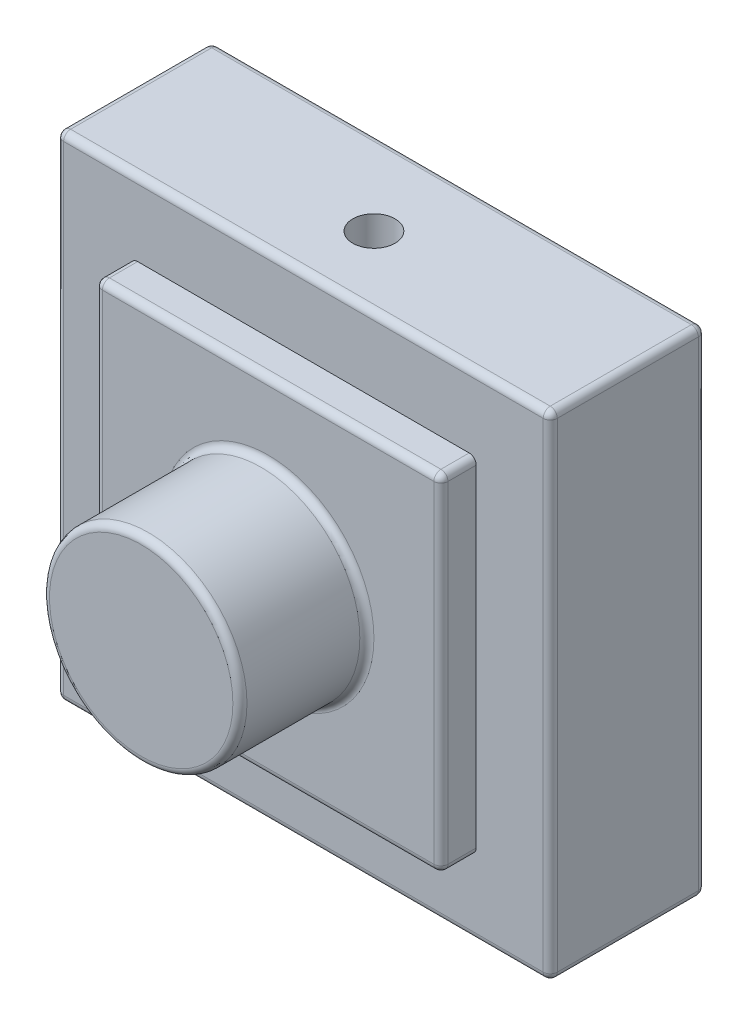
SolidWorks part; units mm, degrees
ref_plane "Front Plane" through (0, 0, 0) normal (0, 0, 1) x (1, 0, 0)
ref_plane "Top Plane" through (0, 0, 0) normal (0, 1, 0) x (1, 0, 0)
ref_plane "Right Plane" through (0, 0, 0) normal (1, 0, 0) x (0, 0, -1)
sketch "Sketch1" plane through (0, 0, 0) normal (0, 0, 1) x (1, 0, 0)
  line L1 (-17.5, 17.5) -> (17.5, 17.5)
  line L2 (-17.5, 17.5) -> (-17.5, -17.5)
  line L3 (-17.5, -17.5) -> (17.5, -17.5)
  line L4 (17.5, 17.5) -> (17.5, -17.5)
  line L5 (-17.5, 17.5) -> (17.5, -17.5) construction
  line L6 (-17.5, -17.5) -> (17.5, 17.5) construction
  point P0 (0, 0)
  dimension "D1" = 35
  dimension "D2" = 35
extrude "Boss-Extrude1" add sketch "Sketch1" along normal blind 11
sketch "Sketch2" plane through (0, 17.5, 0) normal (0, 1, 0) x (1, 0, 0)
  line L0 (0, 0) -> (0, -6) construction
  circle A0 centre (0, -6) radius 1.5
  dimension "D2" = 3
  dimension "D1" = 6
extrude "Cut-Extrude1" cut sketch "Sketch2" against normal blind 5
ref_plane "Plane4" through (0, 0, 0) normal (0, 1, 0) x (1, 0, 0)
mirror "Mirror1" about plane through (0, 0, 0) normal (0, 1, 0) of "Cut-Extrude1"
sketch "Sketch3" plane through (0, 0, 11) normal (0, 0, 1) x (1, 0, 0)
  line L1 (-12.25, 12.25) -> (12.25, 12.25)
  line L2 (-12.25, 12.25) -> (-12.25, -12.25)
  line L3 (-12.25, -12.25) -> (12.25, -12.25)
  line L4 (12.25, 12.25) -> (12.25, -12.25)
  line L5 (-12.25, 12.25) -> (12.25, -12.25) construction
  line L6 (-12.25, -12.25) -> (12.25, 12.25) construction
  point P0 (0, 0)
  dimension "D1" = 24.5
  dimension "D2" = 24.5
extrude "Boss-Extrude2" add sketch "Sketch3" along normal blind 2.5
sketch "Sketch4" plane through (0, 0, 13.5) normal (0, 0, 1) x (1, 0, 0)
  circle A0 centre (0, 0) radius 7
  dimension "D1" = 14
extrude "Boss-Extrude3" add sketch "Sketch4" along normal blind 9
fillet "Fillet1" radius 0.5 21 edges at (17.5, 0, 11) (17.5, 0, 0) (-17.5, 0, 0) (0, 17.5, 0) (0, -17.5, 0) (0, -17.5, 11) (-17.5, 0, 11) (0, 12.25, 13.5) (-12.25, 0, 13.5) (0, -12.25, 13.5) (12.25, 0, 13.5) (-12.25, -12.25, 12.25) (-12.25, 12.25, 12.25) (12.25, -12.25, 12.25) (7, 0, 13.5) (12.25, 12.25, 12.25) (-17.5, -17.5, 5.5) (-17.5, 17.5, 5.5) (17.5, -17.5, 5.5) (17.5, 17.5, 5.5) (0, 17.5, 11)
fillet "Fillet2" radius 0.5 1 edges at (7, 0, 22.5)
ref_plane "Plane5" through (0, 0, 22.5) normal (0, 0, 1) x (1, 0, 0)
ref_plane "Plane6" through (0, 0, 2022.5) normal (0, 0, 1) x (1, 0, 0)
sketch "Sketch6" plane through (0, 0, 22.5) normal (0, 0, 1) x (1, 0, 0)
  line L0 (0, 0) -> (0, -20) construction
  line L1 (-5.359, -20) -> (5.359, -20)
  line L2 (5.359, -20) -> (0, 0)
  line L3 (-5.359, -20) -> (0, 0)
  dimension "D1" = 20
  dimension "D2" = 30
sketch "Sketch7" plane through (0, 0, 2022.5) normal (0, 0, 1) x (1, 0, 0)
  line L1 (-536, 536) -> (536, 536)
  line L2 (-536, 536) -> (-536, -536)
  line L3 (-536, -536) -> (536, -536)
  line L4 (536, 536) -> (536, -536)
  line L5 (-536, 536) -> (536, -536) construction
  line L6 (-536, -536) -> (536, 536) construction
  point P0 (0, 0)
  dimension "D1" = 1072
  dimension "D2" = 1072
sketch "Sketch8" plane through (0, 0, 22.5) normal (0, 0, 1) x (1, 0, 0)
  line L0 (-536, 536) -> (536, -536) construction
  line L1 (-0.5, 0.5) -> (0.5, 0.5)
  line L2 (-0.5, 0.5) -> (-0.5, -0.5)
  line L3 (-0.5, -0.5) -> (0.5, -0.5)
  line L4 (0.5, 0.5) -> (0.5, -0.5)
  line L5 (-0.5, 0.5) -> (0.5, -0.5) construction
  line L6 (-0.5, -0.5) -> (0.5, 0.5) construction
  point P0 (0, 0)
  dimension "D1" = 1
